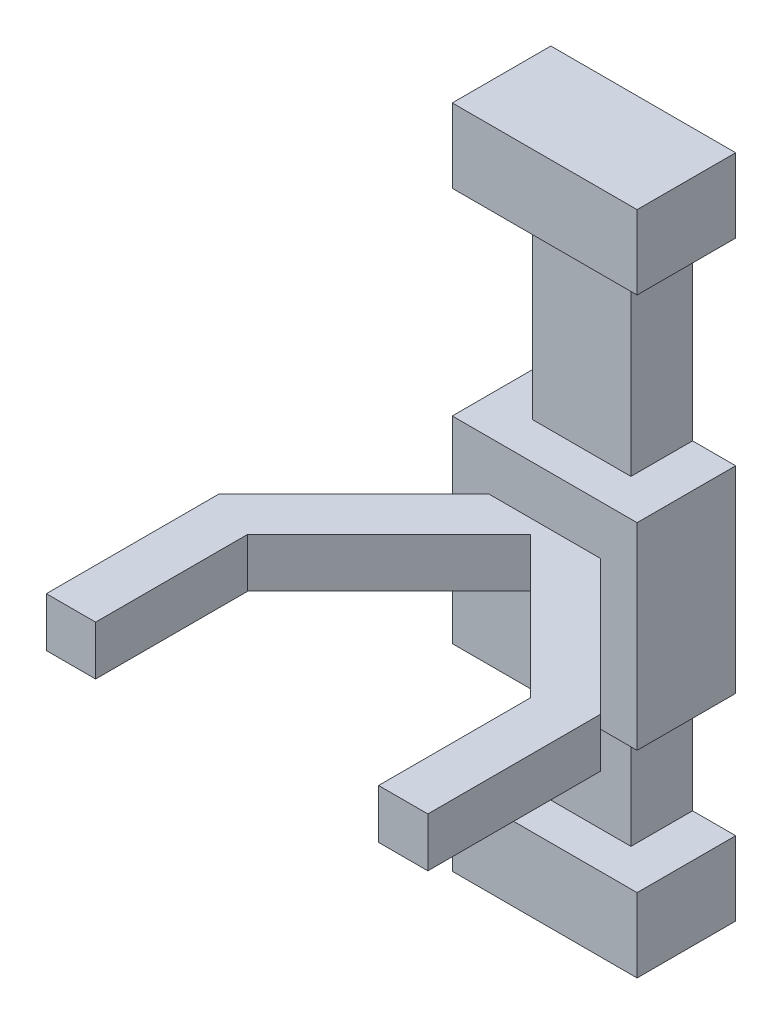
SolidWorks part; units mm, degrees
ref_plane "Front Plane" through (0, 0, 0) normal (0, 0, 1) x (1, 0, 0)
ref_plane "Top Plane" through (0, 0, 0) normal (0, 1, 0) x (1, 0, 0)
ref_plane "Right Plane" through (0, 0, 0) normal (1, 0, 0) x (0, 0, -1)
sketch "Sketch1" plane through (0, 0, 0) normal (0, 0, 1) x (1, 0, 0)
  line L1 (0, 0) -> (40, 0)
  line L2 (0, 0) -> (0, 210)
  line L3 (0, 210) -> (40, 210)
  line L4 (40, 0) -> (40, 210)
  dimension "D1" = 210
  dimension "D2" = 40
extrude "Boss-Extrude1" add sketch "Sketch1" along normal blind 25
sketch "Sketch2" plane through (0, 210, 0) normal (0, 1, 0) x (1, 0, 0)
  line L0 (0, 0) -> (-17.5, 0)
  line L1 (40, 0) -> (57.5, 0)
  line L3 (57.5, 0) -> (-17.5, 0)
  line L4 (57.5, 0) -> (57.5, -40)
  line L5 (57.5, -40) -> (-17.5, -40)
  line L6 (-17.5, 0) -> (-17.5, -40)
  line M4 (40, 0) -> (0, 0)
  line M5 (0, 0) -> (0, -25)
  line M6 (0, -25) -> (40, -25)
  line M7 (40, -25) -> (40, 0)
  dimension "D1" = 17.5
  dimension "D2" = 17.5
  dimension "D3" = 40
extrude "Boss-Extrude2" add sketch "Sketch2" along normal blind 30 contours L0 L6 L5 L4 L1 M7 M6 M5 | M7 M4 M5 M6
sketch "Sketch3" plane through (0, 0, 0) normal (0, -1, 0) x (1, 0, 0)
  line L0 (0, 0) -> (-17.5, 0)
  line L1 (40, 0) -> (57.5, 0)
  line L2 (-17.5, 0) -> (-17.5, 40)
  line L4 (-17.5, 40) -> (57.5, 40)
  line L5 (-17.5, 40) -> (-17.5, 0)
  line L6 (-17.5, 0) -> (57.5, 0)
  line L7 (57.5, 40) -> (57.5, 0)
  line M4 (0, 0) -> (40, 0)
  line M5 (40, 0) -> (40, 25)
  line M6 (40, 25) -> (0, 25)
  line M7 (0, 25) -> (0, 0)
  dimension "D1" = 17.5
  dimension "D2" = 17.5
  dimension "D3" = 40
extrude "Boss-Extrude3" add sketch "Sketch3" along normal blind 30 contours L7 L4 L2 L0 L1 M7 M6 M5 | M7 M4 M5 M6
ref_plane "Plane1" through (0, 50, 0) normal (0, 1, 0) x (1, 0, 0)
sketch "Sketch5" plane through (0, 50, 0) normal (0, 1, 0) x (1, 0, 0)
  line L0 (0, 0) -> (-17.5, 0)
  line L1 (-17.5, 0) -> (-17.5, -40)
  line L4 (-17.5, -40) -> (57.5, -40)
  line L5 (-17.5, -40) -> (-17.5, 0)
  line L6 (-17.5, 0) -> (57.5, 0)
  line L7 (57.5, -40) -> (57.5, 0)
  dimension "D1" = 17.5
  dimension "D2" = 40
  dimension "D3" = 75
extrude "Boss-Extrude4" add sketch "Sketch5" along normal blind 80 contours L4 L7 L6 L0 L1
ref_plane "Plane2" through (11.25, 0, 11.25) normal (0.7071, 0, 0.7071) x (0.7071, 0, -0.7071)
ref_plane "Plane3" through (8.75, 0, -8.75) normal (-0.7071, 0, 0.7071) x (0.7071, 0, 0.7071)
sketch "Sketch6" plane through (11.25, 0, 11.25) normal (0.7071, 0, 0.7071) x (0.7071, 0, -0.7071)
  line L0 (-40.6586, 90) -> (44.3414, 90)
  line L1 (-40.6586, 130) -> (-40.6586, 50) construction
  line L2 (1.8414, 90) -> (1.8414, 110)
  line L4 (1.8414, 90) -> (-18.1586, 90)
  line L5 (1.8414, 90) -> (1.8414, 110)
  line L6 (1.8414, 110) -> (-18.1586, 110)
  line L7 (-18.1586, 90) -> (-18.1586, 110)
  dimension "D1" = 85
  dimension "D2" = 20
  dimension "D3" = 20
extrude "Boss-Extrude5" add sketch "Sketch6" along normal blind 120 contours L7 L0 L2 L6
sketch "Sketch7" plane through (8.75, 0, -8.75) normal (-0.7071, 0, 0.7071) x (0.7071, 0, 0.7071)
  line L0 (68.9429, 90) -> (-16.0571, 90)
  line L1 (68.9429, 130) -> (68.9429, 50) construction
  line L2 (26.4429, 90) -> (26.4429, 110)
  line L4 (26.4429, 110) -> (46.4429, 110)
  line L5 (26.4429, 110) -> (26.4429, 90)
  line L6 (26.4429, 90) -> (46.4429, 90)
  line L7 (46.4429, 110) -> (46.4429, 90)
  dimension "D1" = 85
  dimension "D2" = 20
  dimension "D3" = 20
extrude "Boss-Extrude6" add sketch "Sketch7" along normal blind 120 contours L7 L4 L2 L0
ref_plane "Plane4" through (0, 0, 94.8008) normal (0, 0, 1) x (1, 0, 0)
sketch "Sketch8" plane through (0, 0, 94.8008) normal (0, 0, 1) x (1, 0, 0)
  line L1 (-57.4049, 110) -> (-37.4049, 110)
  line L2 (-57.4049, 110) -> (-57.4049, 90)
  line L3 (-57.4049, 90) -> (-37.4049, 90)
  line L4 (-37.4049, 110) -> (-37.4049, 90)
  line L5 (97.4049, 110) -> (77.4049, 110)
  line L6 (97.4049, 110) -> (97.4049, 90)
  line L7 (97.4049, 90) -> (77.4049, 90)
  line L8 (77.4049, 110) -> (77.4049, 90)
  dimension "D1" = 20
  dimension "D2" = 20
  dimension "D3" = 20
  dimension "D4" = 20
extrude "Boss-Extrude7" add sketch "Sketch8" along normal blind 70
